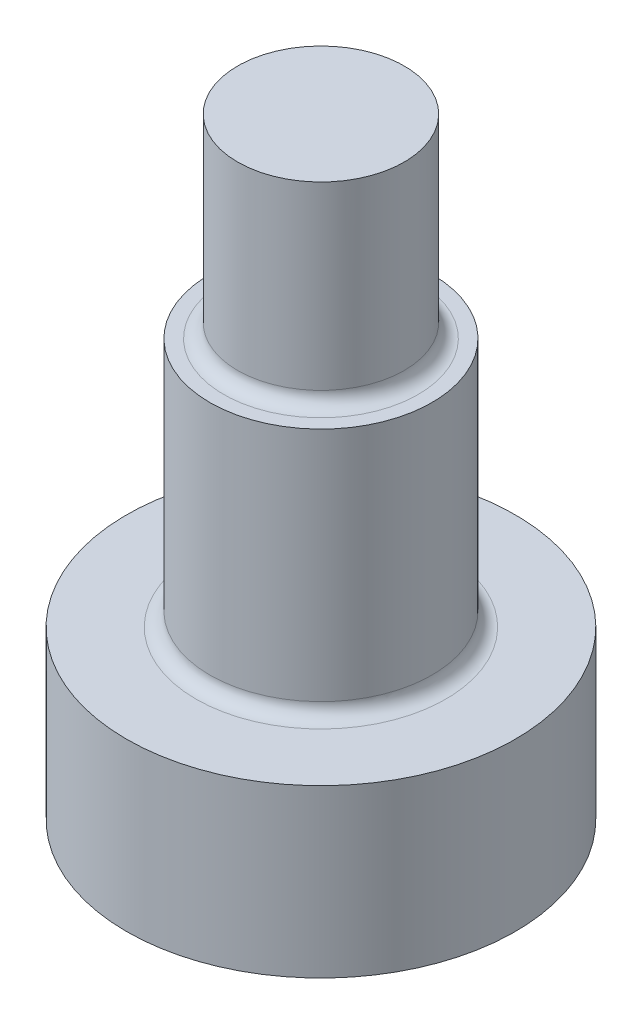
SolidWorks part; units mm, degrees
material "Chrome Stainless Steel"
ref_plane "Front Plane" through (0, 0, 0) normal (0, 0, 1) x (1, 0, 0)
ref_plane "Top Plane" through (0, 0, 0) normal (0, 1, 0) x (1, 0, 0)
ref_plane "Right Plane" through (0, 0, 0) normal (1, 0, 0) x (0, 0, -1)
sketch "Sketch1" plane through (0, 0, 0) normal (0, 0, 1) x (1, 0, 0)
  line L0 (0, 0) -> (7, 0)
  line L1 (55, 0) -> (-55, 0) construction
  line L2 (7, 0) -> (7, 6)
  line L3 (7, 6) -> (4, 6)
  line L4 (4, 6) -> (4, 15)
  line L5 (4, 15) -> (3, 15)
  line L6 (0, -55) -> (0, 55) construction
  line L7 (0, 22) -> (0, 0)
  line L8 (3, 15) -> (3, 22)
  line L9 (3, 22) -> (0, 22)
  dimension "D1" = 6
  dimension "D2" = 7
  dimension "D3" = 4
  dimension "D4" = 3
  dimension "D5" = 16
  dimension "D6" = 7
revolve "Revolve1" add sketch "Sketch1" angle 360 about L7
sketch "Sketch2" plane through (0, 0, 0) normal (0, -1, 0) x (1, 0, 0)
  line L1 (0, -4.6188) -> (4, -2.3094)
  line L2 (4, -2.3094) -> (4, 2.3094)
  line L3 (4, 2.3094) -> (0, 4.6188)
  line L4 (0, 4.6188) -> (-4, 2.3094)
  line L5 (-4, 2.3094) -> (-4, -2.3094)
  line L6 (-4, -2.3094) -> (0, -4.6188)
  circle A0 centre (0, 0) radius 4 construction
  dimension "D1" = 8
extrude "Cut-Extrude1" cut sketch "Sketch2" against normal blind 2
fillet "Fillet1" radius 0.5 1 edges at (0, 6, 4)
fillet "Fillet2" radius 0.5 1 edges at (0, 15, 3)
